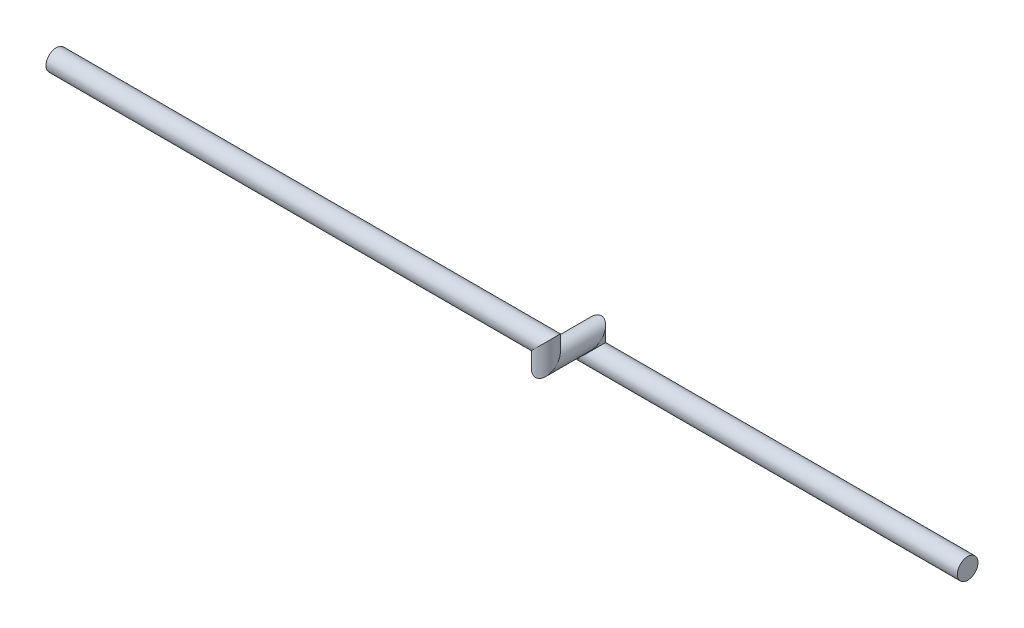
SolidWorks part; units mm, degrees
ref_plane "Alzado" through (0, 0, 0) normal (0, 0, 1) x (1, 0, 0)
ref_plane "Planta" through (0, 0, 0) normal (0, 1, 0) x (1, 0, 0)
ref_plane "Vista lateral" through (0, 0, 0) normal (1, 0, 0) x (0, 0, -1)
sketch3d "Croquis3D1"
  line L0 (0, 0, 0) -> (-500, 0, 0)
  line L1 (-500, 0, 0) -> (-500, 20, 0)
  line L2 (-500, 20, 0) -> (-500, 20, 60)
  line L3 (-500, 20, 60) -> (-500, 40, 60)
  line L4 (-500, 40, 60) -> (-1150, 40, 60)
  dimension "D1" = 500
  dimension "D2" = 20
  dimension "D3" = 60
  dimension "D4" = 20
  dimension "D5" = 650
sketch "Croquis1" plane through (0, 0, 0) normal (1, 0, 0) x (0, 0, -1)
  circle A0 centre (0, 0) radius 13.7
  dimension "D1" = 27.4
sweep "Barrer1" add profiles "Croquis1" path "Croquis3D1"
